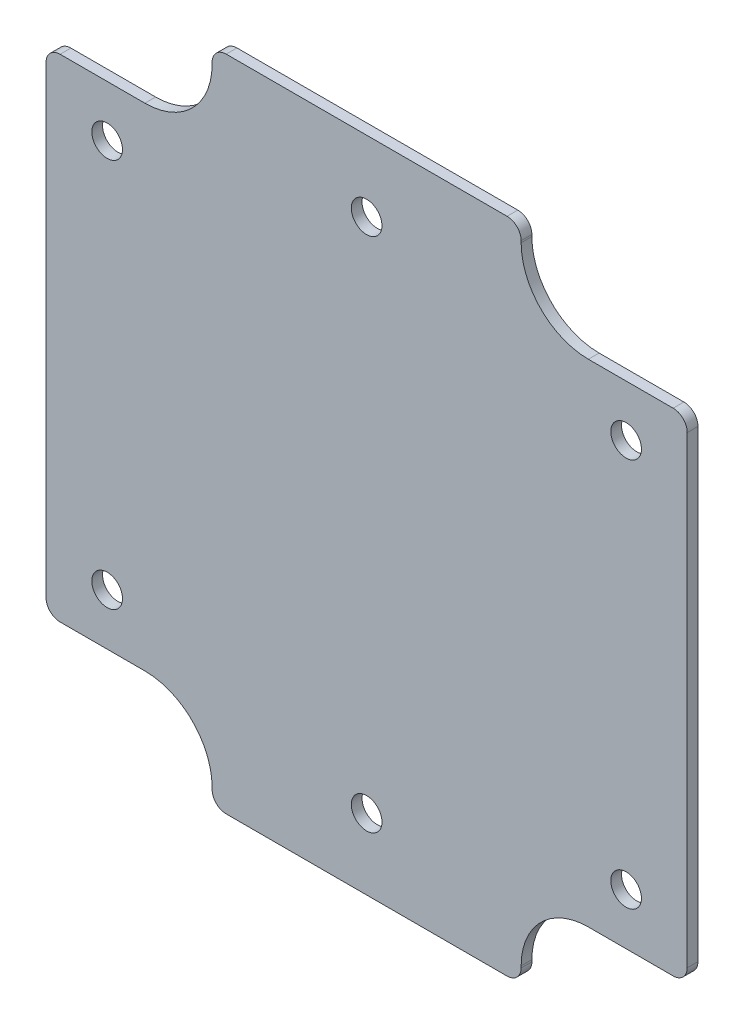
SolidWorks part; units mm, degrees
ref_plane "Front Plane" through (0, 0, 0) normal (0, 0, 1) x (1, 0, 0)
ref_plane "Top Plane" through (0, 0, 0) normal (0, 1, 0) x (1, 0, 0)
ref_plane "Right Plane" through (0, 0, 0) normal (1, 0, 0) x (0, 0, -1)
sketch "Sketch1" plane through (0, 0, 0) normal (0, 0, 1) x (1, 0, 0)
  line L0 (71.6788, 0) -> (0, 0) construction
  line L5 (35.8394, -36.7792) -> (35.8394, 0) construction
  line L6 (71.6788, -27.4828) -> (71.6788, 27.4828)
  line L7 (71.6788, -27.4828) -> (53.1114, -27.4828)
  line L8 (53.1114, -27.4828) -> (53.1114, -36.7792)
  line L9 (53.1114, -36.7792) -> (18.5674, -36.7792)
  line L10 (18.5674, -36.7792) -> (18.5674, -27.4828)
  line L11 (18.5674, -27.4828) -> (0, -27.4828)
  line L12 (0, -27.4828) -> (0, 27.4828)
  line L13 (18.5674, 27.4828) -> (0, 27.4828)
  line L14 (18.5674, 36.7792) -> (18.5674, 27.4828)
  line L15 (53.1114, 36.7792) -> (18.5674, 36.7792)
  line L16 (53.1114, 27.4828) -> (53.1114, 36.7792)
  line L17 (71.6788, 27.4828) -> (53.1114, 27.4828)
  circle A4 centre (64.8462, -21.7424) radius 1.7145
  circle A5 centre (6.8326, -21.7424) radius 1.7145
  circle A6 centre (6.8326, 21.7424) radius 1.7145
  circle A7 centre (64.8462, 21.7424) radius 1.7145
  circle A8 centre (35.8394, -28.8671) radius 1.7145
  circle A9 centre (35.8394, 28.8671) radius 1.7145
  dimension "D5" = 3.429
  dimension "D8" = 3.429
  dimension "D1" = 71.6788
  dimension "D2" = 34.544
  dimension "D3" = 9.2964
  dimension "D4" = 36.7792
  dimension "D6" = 21.7424
  dimension "D7" = 29.0068
  dimension "D9" = 28.8671
extrude "MainBody" add sketch "Sketch1" along normal blind 1.2
fillet "LargeRounds" radius 7.5184 4 edges at (53.1114, -27.4828, 0.6) (18.5674, -27.4828, 0.6) (53.1114, 27.4828, 0.6) (18.5674, 27.4828, 0.6)
fillet "SmallRounds" radius 1.5748 8 edges at (18.5674, -36.7792, 0.6) (53.1114, -36.7792, 0.6) (71.6788, -27.4828, 0.6) (71.6788, 27.4828, 0.6) (53.1114, 36.7792, 0.6) (18.5674, 36.7792, 0.6) (0, 27.4828, 0.6) (0, -27.4828, 0.6)
